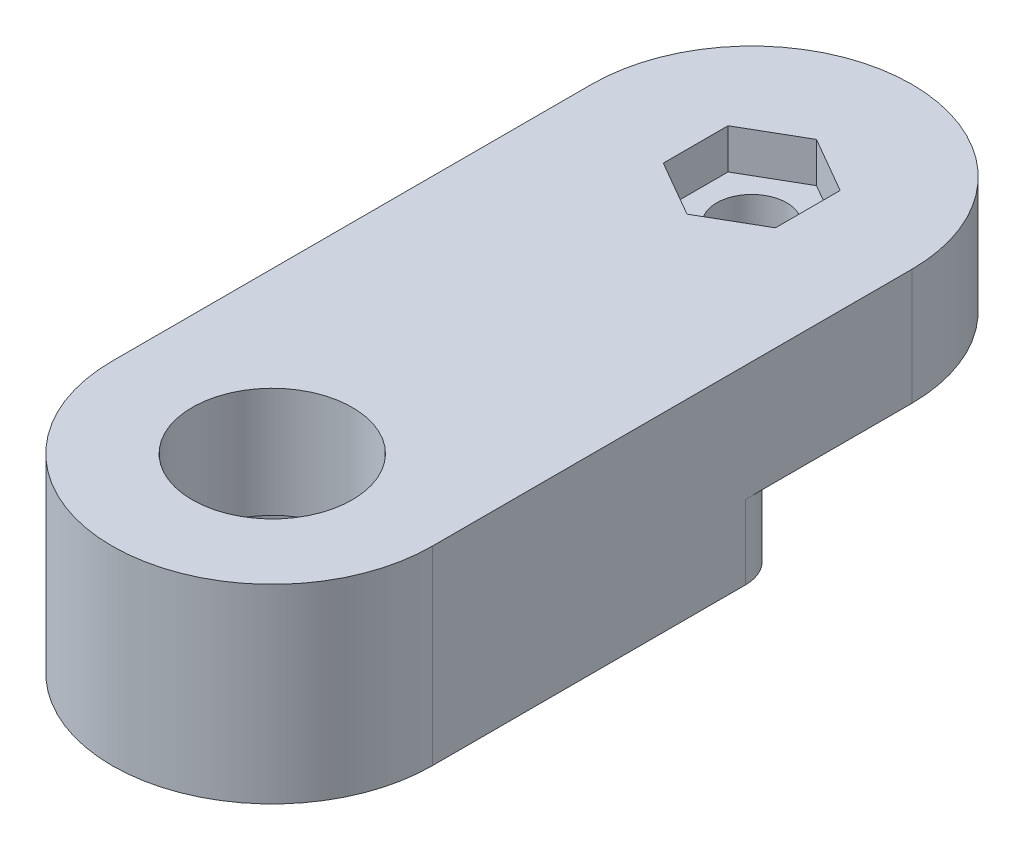
SolidWorks part; units mm, degrees
ref_plane "Front Plane" through (0, 0, 0) normal (0, 0, 1) x (1, 0, 0)
ref_plane "Top Plane" through (0, 0, 0) normal (0, 1, 0) x (1, 0, 0)
ref_plane "Right Plane" through (0, 0, 0) normal (1, 0, 0) x (0, 0, -1)
sketch "Sketch1" plane through (0, 0, 0) normal (0, 1, 0) x (1, 0, 0)
  line L0 (0, 27.4685) -> (0, -33.8565) construction
  line L1 (-8, 0) -> (-8, 23.95)
  line L2 (8, 0) -> (8, 23.95)
  circle A0 centre (0, 0) radius 8
  circle A1 centre (0, 23.95) radius 8
  circle A2 centre (0, 0) radius 5.15
  dimension "D1" = 16
  dimension "D4" = 10.3
  dimension "D2" = 23.95
extrude "Boss-Extrude1" add sketch "Sketch1" along normal blind 4
sketch "Sketch2" plane through (0, 4, 0) normal (0, 1, 0) x (1, 0, 0)
  line L2 (-8, 23.95) -> (-8, 0)
  line L3 (8, 0) -> (8, 23.95)
  line L4 (-8, 23.95) -> (-8, 0)
  line L5 (8, 0) -> (8, 23.95)
  circle A0 centre (0, 0) radius 4
  arc A3 (-8, 0) -> (8, 0) centre (0, 0) ccw
  arc A4 (8, 23.95) -> (-8, 23.95) centre (0, 23.95) ccw
  arc A5 (-8, 0) -> (8, 0) centre (0, 0) ccw
  arc A6 (8, 23.95) -> (-8, 23.95) centre (0, 23.95) ccw
  dimension "D1" = 8
  dimension "D2" = 0
extrude "Boss-Extrude2" add sketch "Sketch2" along normal offset from surface (5.5 mm away) 9.5 up to face at (0, 0, -11.975)
sketch "Sketch3" plane through (0, 0, 0) normal (0, 1, 0) x (1, 0, 0)
  circle A0 centre (0, 23.95) radius 8.25
  arc A2 (8, 23.95) -> (-8, 23.95) centre (0, 23.95) ccw construction
  dimension "D1" = 16.5
extrude "Cut-Extrude1" cut sketch "Sketch3" along normal offset from surface (3.7 mm away) 5.8 up to face at (0, 9.5, 4)
sketch "Sketch4" plane through (0, 3.7, 0) normal (0, -1, 0) x (1, 0, 0)
  circle A0 centre (0, -23.95) radius 1.75
  dimension "D1" = 3.5
extrude "Cut-Extrude2" cut sketch "Sketch4" against normal up to next
sketch "Sketch5" plane through (0, 3.7, 0) normal (0, -1, 0) x (1, 0, 0)
  circle A0 centre (0, -23.95) radius 4.1
  circle A1 centre (0, -23.95) radius 1.75 construction
  circle A2 centre (0, -23.95) radius 1.75
  dimension "D1" = 8.2
extrude "Boss-Extrude3" add sketch "Sketch5" along normal blind 0.2
sketch "Sketch6" plane through (0, 9.5, 0) normal (0, 1, 0) x (1, 0, 0)
  line L0 (-8, 23.95) -> (-8, 0) construction
  line L1 (0, 20.7168) -> (2.8, 22.3334)
  line L2 (2.8, 22.3334) -> (2.8, 25.5666)
  line L3 (2.8, 25.5666) -> (0, 27.1832)
  line L4 (0, 27.1832) -> (-2.8, 25.5666)
  line L5 (-2.8, 25.5666) -> (-2.8, 22.3334)
  line L6 (-2.8, 22.3334) -> (0, 20.7168)
  circle A0 centre (0, 23.95) radius 2.8 construction
  dimension "D1" = 5.6
extrude "Cut-Extrude3" cut sketch "Sketch6" against normal blind 2
fillet "Fillet1" radius 2 2 edges at (-8, 1.85, -21.9344) (8, 1.85, -21.9344)
